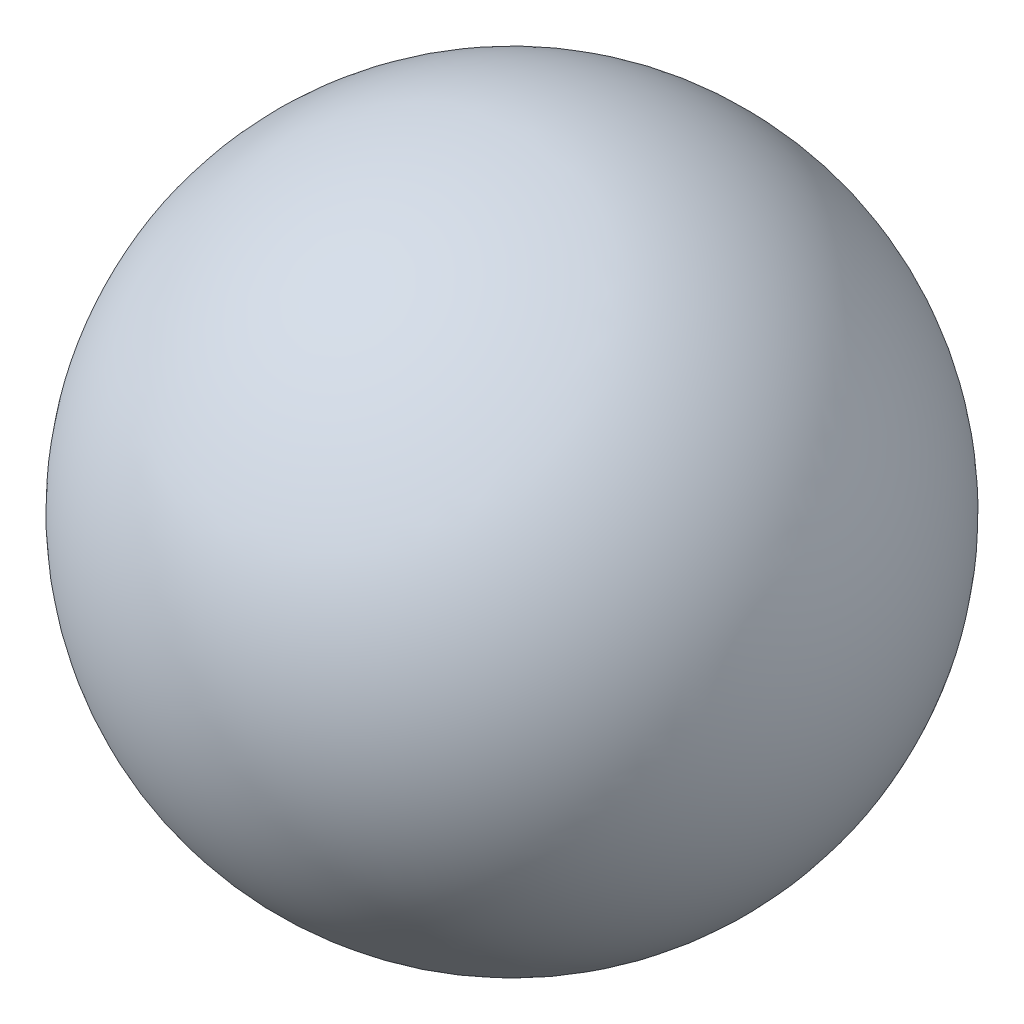
SolidWorks part; units mm, degrees
ref_plane "Front Plane" through (0, 0, 0) normal (0, 0, 1) x (1, 0, 0)
ref_plane "Top Plane" through (0, 0, 0) normal (0, 1, 0) x (1, 0, 0)
ref_plane "Right Plane" through (0, 0, 0) normal (1, 0, 0) x (0, 0, -1)
sketch "Sketch1" plane through (0, 0, 0) normal (0, 0, 1) x (1, 0, 0)
  line L0 (-12.6528, 0.0005) -> (12.7457, 0.2765)
  arc A1 (-12.6528, 0.0005) -> (12.7457, 0.2765) centre (0.0465, 0.1385) ccw
  dimension "D1" = 12.7
revolve "Revolve1" add sketch "Sketch1" angle 360 about L0
